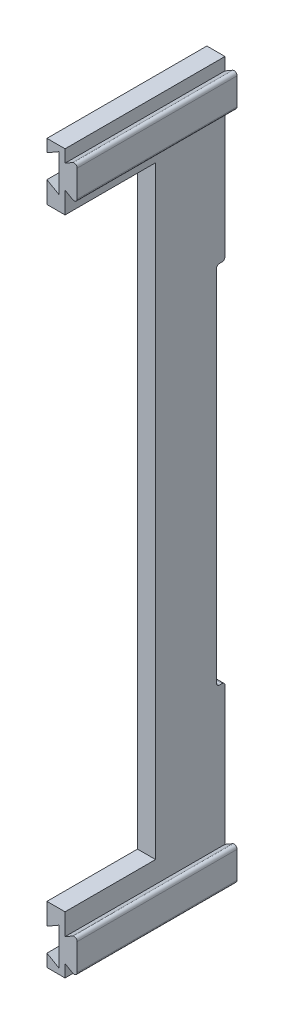
SolidWorks part; units mm, degrees
ref_plane "Front Plane" through (0, 0, 0) normal (0, 0, 1) x (1, 0, 0)
ref_plane "Top Plane" through (0, 0, 0) normal (0, 1, 0) x (1, 0, 0)
ref_plane "Right Plane" through (0, 0, 0) normal (1, 0, 0) x (0, 0, -1)
sketch "Sketch2" plane through (0, 0, 0) normal (0, 0, 1) x (1, 0, 0)
  line L0 (0, 0) -> (0, -4.14)
  line L2 (6, -8.7233) -> (6, 0) construction
  line L3 (6, 0) -> (0, 0)
  line L4 (0, 0) -> (0, -4.14) construction
  line L5 (0, -19) -> (0, -11.86) construction
  line L6 (0, -4.14) -> (4.0097, -1.825) construction
  line L7 (4.0097, -1.825) -> (4.0097, -14.175)
  line L8 (0, -4.14) -> (4.0097, -1.825)
  line L9 (0, -11.86) -> (4.0097, -14.175)
  line L10 (0, -19) -> (0, -219)
  line L11 (0, -119) -> (59.9435, -119) construction
  line L12 (6, -238) -> (0, -238)
  line L13 (6, -229.2767) -> (6, -238) construction
  line L15 (0, -238) -> (0, -233.86)
  line L16 (0, -226.14) -> (4.0097, -223.825)
  line L17 (4.0097, -236.175) -> (4.0097, -223.825)
  line L18 (0, -233.86) -> (4.0097, -236.175)
  line L19 (0, -226.14) -> (0, -219)
  line L20 (0, -11.86) -> (0, -19)
  line L21 (6, -229.2767) -> (6, -8.7233) construction
  line L22 (10.0097, -1.825) -> (10.0097, -14.175)
  line L23 (6, -11.86) -> (10.0097, -14.175)
  line L24 (6, -4.14) -> (10.0097, -1.825)
  line L25 (6, -226.14) -> (10.0097, -223.825)
  line L26 (10.0097, -236.175) -> (10.0097, -223.825)
  line L27 (6, -233.86) -> (10.0097, -236.175)
  line L28 (6, 0) -> (6, -4.14)
  line L29 (6, -11.86) -> (6, -226.14)
  line L30 (6, -233.86) -> (6, -238)
  dimension "D1" = 19
  dimension "D2" = 11.9
  dimension "D3" = 4.14
  dimension "D4" = 7.14
  dimension "D5" = 60
  dimension "D6" = 60
  dimension "D7" = 12.35
  dimension "D8" = 200
  dimension "D9" = 6
  dimension "D10" = 2
extrude "Boss-Extrude1" add sketch "Sketch2" along normal blind 53
sketch "Sketch3" plane through (0, 0, 0) normal (1, 0, 0) x (0, 0, -1)
  line L0 (0, -119) -> (0, -58.5)
  line L3 (0, -11.86) -> (0, -226.14) construction
  line L4 (0, -119) -> (0, -179.5)
  line L5 (0, -58.5) -> (-2.8, -58.5)
  line L6 (-2.8, -58.5) -> (-2.8, -179.5)
  line L7 (-2.8, -179.5) -> (0, -179.5)
  point P5 (-5.9, -144.9585)
  point P6 (0, -158.9397)
  dimension "D1" = 121
  dimension "D2" = 2.8
  dimension "D3" = 60.5
extrude "Cut-Extrude1" cut sketch "Sketch3" along normal blind 52
fillet "Fillet1" radius 1 7 edges at (0, -58.5, 1.4) (0, -179.5, 1.4) (3, -58.5, 0) (3, -58.5, 2.8) (0, -119, 2.8) (3, -179.5, 2.8) (3, -179.5, 0)
sketch "Sketch4" plane through (6, 0, 0) normal (1, 0, 0) x (0, 0, -1)
  line L0 (-53, -226.14) -> (-53, -11.86) construction
  line L1 (-53, -219) -> (-23, -219)
  line L2 (-53, -219) -> (-53, -19)
  line L3 (-53, -19) -> (-23, -19)
  line L4 (-23, -219) -> (-23, -19)
  line L5 (-53, 0) -> (0, 0) construction
  line L6 (-53, -238) -> (0, -238) construction
  point P10 (-26.5, -238)
  dimension "D1" = 19
  dimension "D2" = 19
  dimension "D3" = 30
fillet "Fillet2" [suppressed] radius 1
fillet "Fillet3" radius 1 4 edges at (10.0097, -223.825, 26.5) (10.0097, -236.175, 26.5) (10.0097, -1.825, 26.5) (10.0097, -14.175, 26.5)
extrude "Cut-Extrude2" cut sketch "Sketch4" against normal blind 10
